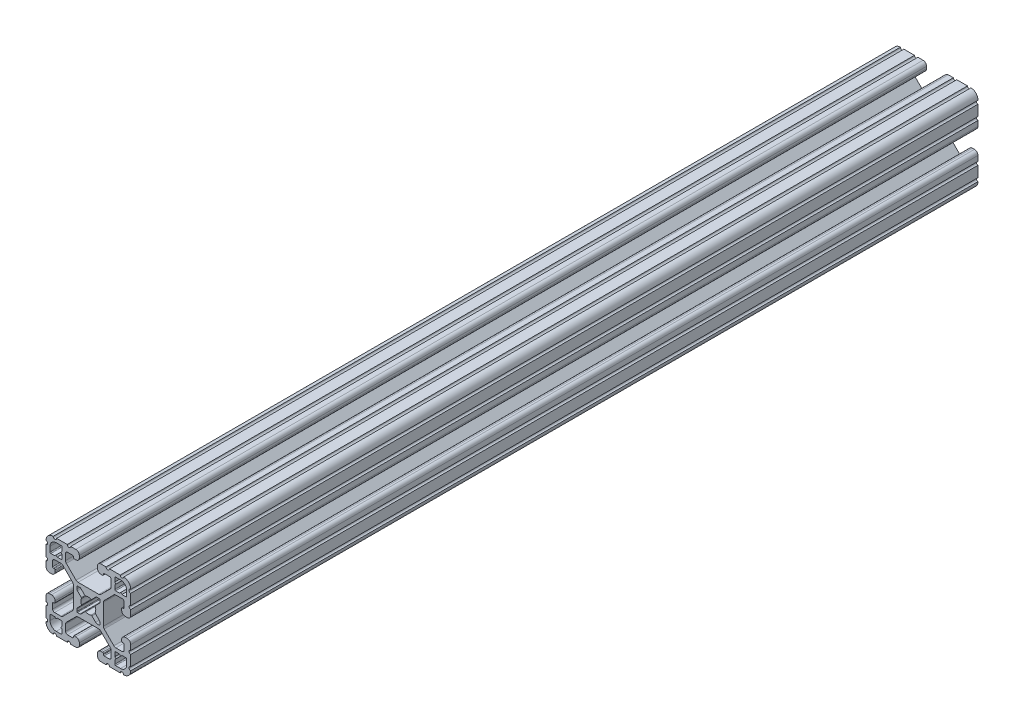
SolidWorks part; units mm, degrees
ref_plane "Front Plane" through (0, 0, 0) normal (0, 0, 1) x (1, 0, 0)
ref_plane "Top Plane" through (0, 0, 0) normal (0, 1, 0) x (1, 0, 0)
ref_plane "Right Plane" through (0, 0, 0) normal (1, 0, 0) x (0, 0, -1)
sketch "Sketch1" plane through (0, 0, 0) normal (0, 0, 1) x (1, 0, 0)
  line L0 (1.5823, 3.1988) -> (3.2921, 4.9085)
  line L1 (3.9207, 5.1689) -> (4.9149, 5.1689)
  line L2 (5.1689, 4.9149) -> (5.1689, 3.9207)
  line L3 (4.9085, 3.2921) -> (3.1988, 1.5823)
  line L4 (3.1988, -1.5823) -> (4.9085, -3.2921)
  line L5 (5.1689, -3.9207) -> (5.1689, -4.9149)
  line L6 (4.9149, -5.1689) -> (3.9207, -5.1689)
  line L7 (3.2921, -4.9085) -> (1.5823, -3.1988)
  line L8 (-1.5823, -3.1988) -> (-3.2921, -4.9085)
  line L9 (-3.9207, -5.1689) -> (-4.9149, -5.1689)
  line L10 (-5.1689, -4.9149) -> (-5.1689, -3.9207)
  line L11 (-4.9085, -3.2921) -> (-3.1988, -1.5823)
  line L12 (-3.1988, 1.5823) -> (-4.9085, 3.2921)
  line L13 (-5.1689, 3.9207) -> (-5.1689, 4.9149)
  line L14 (-4.9149, 5.1689) -> (-3.9207, 5.1689)
  line L15 (-3.2921, 4.9085) -> (-1.5823, 3.1988)
  line L16 (-11.8669, 14.0194) -> (-11.8669, 12.2479)
  line L17 (-12.2479, 11.8669) -> (-14.0195, 11.8669)
  line L18 (-14.0213, 11.8676) -> (-14.5575, 12.4039)
  line L19 (-14.5611, 12.4039) -> (-15.0973, 11.8676)
  line L20 (-15.0991, 11.8669) -> (-16.8707, 11.8669)
  line L21 (-17.2517, 12.2479) -> (-17.2517, 14.4577)
  line L22 (-14.4577, 17.2517) -> (-12.2479, 17.2517)
  line L23 (-11.8669, 16.8707) -> (-11.8669, 15.0991)
  line L24 (-11.8676, 15.0973) -> (-12.4039, 14.5611)
  line L25 (-12.4039, 14.5575) -> (-11.8676, 14.0212)
  line L26 (-14.0194, -11.8669) -> (-12.2479, -11.8669)
  line L27 (-11.8669, -12.2479) -> (-11.8669, -14.0195)
  line L28 (-11.8676, -14.0213) -> (-12.4039, -14.5575)
  line L29 (-12.4039, -14.5611) -> (-11.8676, -15.0973)
  line L30 (-11.8669, -15.0991) -> (-11.8669, -16.8707)
  line L31 (-12.2479, -17.2517) -> (-14.4577, -17.2517)
  line L32 (-17.2517, -14.4577) -> (-17.2517, -12.2479)
  line L33 (-16.8707, -11.8669) -> (-15.0991, -11.8669)
  line L34 (-15.0973, -11.8676) -> (-14.5611, -12.4039)
  line L35 (-14.5575, -12.4039) -> (-14.0212, -11.8676)
  line L36 (11.8669, -14.0194) -> (11.8669, -12.2479)
  line L37 (12.2479, -11.8669) -> (14.0195, -11.8669)
  line L38 (14.0213, -11.8676) -> (14.5575, -12.4039)
  line L39 (14.5611, -12.4039) -> (15.0973, -11.8676)
  line L40 (15.0991, -11.8669) -> (16.8707, -11.8669)
  line L41 (17.2517, -12.2479) -> (17.2517, -14.4577)
  line L42 (14.4577, -17.2517) -> (12.2479, -17.2517)
  line L43 (11.8669, -16.8707) -> (11.8669, -15.0991)
  line L44 (11.8676, -15.0973) -> (12.4039, -14.5611)
  line L45 (12.4039, -14.5575) -> (11.8676, -14.0212)
  line L46 (14.0194, 11.8669) -> (12.2479, 11.8669)
  line L47 (11.8669, 12.2479) -> (11.8669, 14.0195)
  line L48 (11.8676, 14.0213) -> (12.4039, 14.5575)
  line L49 (12.4039, 14.5611) -> (11.8676, 15.0973)
  line L50 (11.8669, 15.0991) -> (11.8669, 16.8707)
  line L51 (12.2479, 17.2517) -> (14.4577, 17.2517)
  line L52 (17.2517, 14.4577) -> (17.2517, 12.2479)
  line L53 (16.8707, 11.8669) -> (15.0991, 11.8669)
  line L54 (15.0973, 11.8676) -> (14.5611, 12.4039)
  line L55 (14.5575, 12.4039) -> (14.0212, 11.8676)
  line L56 (6.3498, -14.9848) -> (5.6531, -14.9848)
  line L57 (4.0778, -16.5601) -> (4.0778, -17.4747)
  line L58 (5.6531, -19.05) -> (7.9756, -19.05)
  line L59 (9.4996, -19.05) -> (14.2981, -19.05)
  line L60 (19.05, -14.3256) -> (19.05, -9.4996)
  line L61 (19.05, -7.9756) -> (19.05, -5.6531)
  line L62 (17.4747, -4.0778) -> (16.5601, -4.0778)
  line L63 (14.9848, -5.6531) -> (14.9848, -6.3498)
  line L64 (15.3661, -6.731) -> (15.6969, -6.731)
  line L65 (16.0782, -7.1122) -> (16.0782, -9.3968)
  line L66 (15.1881, -10.287) -> (12.3526, -10.2871)
  line L67 (11.4535, -9.9142) -> (7.1147, -5.5659)
  line L68 (6.7437, -4.6689) -> (6.7437, 4.6414)
  line L69 (7.1147, 5.5384) -> (11.481, 9.9142)
  line L70 (12.38, 10.2871) -> (15.1881, 10.287)
  line L71 (16.0782, 9.3968) -> (16.0782, 7.1122)
  line L72 (15.6969, 6.731) -> (15.3661, 6.731)
  line L73 (14.9848, 6.3498) -> (14.9848, 5.6531)
  line L74 (16.5601, 4.0778) -> (17.4747, 4.0778)
  line L75 (19.05, 5.6531) -> (19.05, 7.9756)
  line L76 (19.05, 9.4996) -> (19.05, 14.2981)
  line L77 (14.3256, 19.05) -> (9.4996, 19.05)
  line L78 (7.9756, 19.05) -> (5.6531, 19.05)
  line L79 (4.0778, 17.4747) -> (4.0778, 16.5601)
  line L80 (5.6531, 14.9848) -> (6.3498, 14.9848)
  line L81 (6.731, 15.3661) -> (6.731, 15.6969)
  line L82 (7.1122, 16.0782) -> (9.3968, 16.0782)
  line L83 (10.287, 15.1881) -> (10.2871, 12.3526)
  line L84 (9.9142, 11.4535) -> (5.5659, 7.1147)
  line L85 (4.6689, 6.7437) -> (-4.6414, 6.7437)
  line L86 (-5.5384, 7.1147) -> (-9.9142, 11.481)
  line L87 (-10.2871, 12.38) -> (-10.287, 15.1881)
  line L88 (-9.3968, 16.0782) -> (-7.1122, 16.0782)
  line L89 (-6.731, 15.6969) -> (-6.731, 15.3661)
  line L90 (-6.3498, 14.9848) -> (-5.6531, 14.9848)
  line L91 (-4.0778, 16.5601) -> (-4.0778, 17.4747)
  line L92 (-5.6531, 19.05) -> (-7.9756, 19.05)
  line L93 (-9.4996, 19.05) -> (-14.2981, 19.05)
  line L94 (-19.05, 14.3256) -> (-19.05, 9.4996)
  line L95 (-19.05, 7.9756) -> (-19.05, 5.6531)
  line L96 (-17.4747, 4.0778) -> (-16.5601, 4.0778)
  line L97 (-14.9848, 5.6531) -> (-14.9848, 6.3498)
  line L98 (-15.3661, 6.731) -> (-15.6969, 6.731)
  line L99 (-16.0782, 7.1122) -> (-16.0782, 9.3968)
  line L100 (-15.1881, 10.287) -> (-12.3526, 10.2871)
  line L101 (-11.4535, 9.9142) -> (-7.1147, 5.5659)
  line L102 (-6.7437, 4.6689) -> (-6.7437, -4.6414)
  line L103 (-7.1147, -5.5384) -> (-11.481, -9.9142)
  line L104 (-12.38, -10.2871) -> (-15.1881, -10.287)
  line L105 (-16.0782, -9.3968) -> (-16.0782, -7.1122)
  line L106 (-15.6969, -6.731) -> (-15.3661, -6.731)
  line L107 (-14.9848, -6.3498) -> (-14.9848, -5.6531)
  line L108 (-16.5601, -4.0778) -> (-17.4747, -4.0778)
  line L109 (-19.05, -5.6531) -> (-19.05, -7.9756)
  line L110 (-19.05, -9.4996) -> (-19.05, -14.2981)
  line L111 (-14.3256, -19.05) -> (-9.4996, -19.05)
  line L112 (-7.9756, -19.05) -> (-5.6531, -19.05)
  line L113 (-4.0778, -17.4747) -> (-4.0778, -16.5601)
  line L114 (-5.6531, -14.9848) -> (-6.3498, -14.9848)
  line L115 (-6.731, -15.3661) -> (-6.731, -15.6969)
  line L116 (-7.1122, -16.0782) -> (-9.3968, -16.0782)
  line L117 (-10.287, -15.1881) -> (-10.2871, -12.3526)
  line L118 (-9.9142, -11.4535) -> (-5.5659, -7.1147)
  line L119 (-4.6689, -6.7437) -> (4.6414, -6.7437)
  line L120 (5.5384, -7.1147) -> (9.9142, -11.481)
  line L121 (10.2871, -12.38) -> (10.287, -15.1881)
  line L122 (9.3968, -16.0782) -> (7.1122, -16.0782)
  line L123 (6.731, -15.6969) -> (6.731, -15.3661)
  arc A0 (1.178, 3.1119) -> (1.5823, 3.1988) centre (1.3129, 3.4682) ccw
  arc A1 (3.9207, 5.1689) -> (3.2921, 4.9085) centre (3.9207, 4.2799) ccw
  arc A2 (5.1689, 4.9149) -> (4.9149, 5.1689) centre (4.9149, 4.9149) ccw
  arc A3 (4.9085, 3.2921) -> (5.1689, 3.9207) centre (4.2799, 3.9207) ccw
  arc A4 (3.1988, 1.5823) -> (3.1119, 1.178) centre (3.4682, 1.3129) ccw
  arc A5 (3.1119, -1.178) -> (3.1119, 1.178) centre (0, 0) ccw
  arc A6 (3.1119, -1.178) -> (3.1988, -1.5823) centre (3.4682, -1.3129) ccw
  arc A7 (5.1689, -3.9207) -> (4.9085, -3.2921) centre (4.2799, -3.9207) ccw
  arc A8 (4.9149, -5.1689) -> (5.1689, -4.9149) centre (4.9149, -4.9149) ccw
  arc A9 (3.2921, -4.9085) -> (3.9207, -5.1689) centre (3.9207, -4.2799) ccw
  arc A10 (1.5823, -3.1988) -> (1.178, -3.1119) centre (1.3129, -3.4682) ccw
  arc A11 (-1.178, -3.1119) -> (1.178, -3.1119) centre (0, 0) ccw
  arc A12 (-1.178, -3.1119) -> (-1.5823, -3.1988) centre (-1.3129, -3.4682) ccw
  arc A13 (-3.9207, -5.1689) -> (-3.2921, -4.9085) centre (-3.9207, -4.2799) ccw
  arc A14 (-5.1689, -4.9149) -> (-4.9149, -5.1689) centre (-4.9149, -4.9149) ccw
  arc A15 (-4.9085, -3.2921) -> (-5.1689, -3.9207) centre (-4.2799, -3.9207) ccw
  arc A16 (-3.1988, -1.5823) -> (-3.1119, -1.178) centre (-3.4682, -1.3129) ccw
  arc A17 (-3.1119, 1.178) -> (-3.1119, -1.178) centre (0, 0) ccw
  arc A18 (-3.1119, 1.178) -> (-3.1988, 1.5823) centre (-3.4682, 1.3129) ccw
  arc A19 (-5.1689, 3.9207) -> (-4.9085, 3.2921) centre (-4.2799, 3.9207) ccw
  arc A20 (-4.9149, 5.1689) -> (-5.1689, 4.9149) centre (-4.9149, 4.9149) ccw
  arc A21 (-3.2921, 4.9085) -> (-3.9207, 5.1689) centre (-3.9207, 4.2799) ccw
  arc A22 (-1.5823, 3.1988) -> (-1.178, 3.1119) centre (-1.3129, 3.4682) ccw
  arc A23 (1.178, 3.1119) -> (-1.178, 3.1119) centre (0, 0) ccw
  arc A24 (-11.8669, 14.0194) -> (-11.8676, 14.0212) centre (-11.8694, 14.0194) ccw
  arc A25 (-12.2479, 11.8669) -> (-11.8669, 12.2479) centre (-12.2479, 12.2479) ccw
  arc A26 (-14.0213, 11.8676) -> (-14.0195, 11.8669) centre (-14.0195, 11.8694) ccw
  arc A27 (-14.5575, 12.4039) -> (-14.5611, 12.4039) centre (-14.5593, 12.4021) ccw
  arc A28 (-15.0991, 11.8669) -> (-15.0973, 11.8676) centre (-15.0991, 11.8694) ccw
  arc A29 (-17.2517, 12.2479) -> (-16.8707, 11.8669) centre (-16.8707, 12.2479) ccw
  arc A30 (-14.4577, 17.2517) -> (-17.2517, 14.4577) centre (-14.4577, 14.4577) ccw
  arc A31 (-11.8669, 16.8707) -> (-12.2479, 17.2517) centre (-12.2479, 16.8707) ccw
  arc A32 (-11.8676, 15.0973) -> (-11.8669, 15.0991) centre (-11.8694, 15.0991) ccw
  arc A33 (-12.4039, 14.5611) -> (-12.4039, 14.5575) centre (-12.4021, 14.5593) ccw
  arc A34 (-14.0194, -11.8669) -> (-14.0212, -11.8676) centre (-14.0194, -11.8694) ccw
  arc A35 (-11.8669, -12.2479) -> (-12.2479, -11.8669) centre (-12.2479, -12.2479) ccw
  arc A36 (-11.8676, -14.0213) -> (-11.8669, -14.0195) centre (-11.8694, -14.0195) ccw
  arc A37 (-12.4039, -14.5575) -> (-12.4039, -14.5611) centre (-12.4021, -14.5593) ccw
  arc A38 (-11.8669, -15.0991) -> (-11.8676, -15.0973) centre (-11.8694, -15.0991) ccw
  arc A39 (-12.2479, -17.2517) -> (-11.8669, -16.8707) centre (-12.2479, -16.8707) ccw
  arc A40 (-17.2517, -14.4577) -> (-14.4577, -17.2517) centre (-14.4577, -14.4577) ccw
  arc A41 (-16.8707, -11.8669) -> (-17.2517, -12.2479) centre (-16.8707, -12.2479) ccw
  arc A42 (-15.0973, -11.8676) -> (-15.0991, -11.8669) centre (-15.0991, -11.8694) ccw
  arc A43 (-14.5611, -12.4039) -> (-14.5575, -12.4039) centre (-14.5593, -12.4021) ccw
  arc A44 (11.8669, -14.0194) -> (11.8676, -14.0212) centre (11.8694, -14.0194) ccw
  arc A45 (12.2479, -11.8669) -> (11.8669, -12.2479) centre (12.2479, -12.2479) ccw
  arc A46 (14.0213, -11.8676) -> (14.0195, -11.8669) centre (14.0195, -11.8694) ccw
  arc A47 (14.5575, -12.4039) -> (14.5611, -12.4039) centre (14.5593, -12.4021) ccw
  arc A48 (15.0991, -11.8669) -> (15.0973, -11.8676) centre (15.0991, -11.8694) ccw
  arc A49 (17.2517, -12.2479) -> (16.8707, -11.8669) centre (16.8707, -12.2479) ccw
  arc A50 (14.4577, -17.2517) -> (17.2517, -14.4577) centre (14.4577, -14.4577) ccw
  arc A51 (11.8669, -16.8707) -> (12.2479, -17.2517) centre (12.2479, -16.8707) ccw
  arc A52 (11.8676, -15.0973) -> (11.8669, -15.0991) centre (11.8694, -15.0991) ccw
  arc A53 (12.4039, -14.5611) -> (12.4039, -14.5575) centre (12.4021, -14.5593) ccw
  arc A54 (14.0194, 11.8669) -> (14.0212, 11.8676) centre (14.0194, 11.8694) ccw
  arc A55 (11.8669, 12.2479) -> (12.2479, 11.8669) centre (12.2479, 12.2479) ccw
  arc A56 (11.8676, 14.0213) -> (11.8669, 14.0195) centre (11.8694, 14.0195) ccw
  arc A57 (12.4039, 14.5575) -> (12.4039, 14.5611) centre (12.4021, 14.5593) ccw
  arc A58 (11.8669, 15.0991) -> (11.8676, 15.0973) centre (11.8694, 15.0991) ccw
  arc A59 (12.2479, 17.2517) -> (11.8669, 16.8707) centre (12.2479, 16.8707) ccw
  arc A60 (17.2517, 14.4577) -> (14.4577, 17.2517) centre (14.4577, 14.4577) ccw
  arc A61 (16.8707, 11.8669) -> (17.2517, 12.2479) centre (16.8707, 12.2479) ccw
  arc A62 (15.0973, 11.8676) -> (15.0991, 11.8669) centre (15.0991, 11.8694) ccw
  arc A63 (14.5611, 12.4039) -> (14.5575, 12.4039) centre (14.5593, 12.4021) ccw
  arc A64 (6.731, -15.3661) -> (6.3498, -14.9848) centre (6.35, -15.3658) ccw
  arc A65 (5.6531, -14.9848) -> (4.0778, -16.5601) centre (5.6526, -16.5596) ccw
  arc A66 (4.0778, -17.4747) -> (5.6531, -19.05) centre (5.6526, -17.4752) ccw
  arc A67 (9.4996, -19.05) -> (7.9756, -19.05) centre (8.7376, -19.05) ccw
  arc A68 (15.8221, -19.0496) -> (14.2981, -19.05) centre (15.0601, -19.05) ccw
  arc A69 (15.8221, -19.0496) -> (19.0499, -15.8496) centre (15.875, -15.875) ccw
  arc A70 (19.05, -14.3256) -> (19.0499, -15.8496) centre (19.05, -15.0876) ccw
  arc A71 (19.05, -7.9756) -> (19.05, -9.4996) centre (19.05, -8.7376) ccw
  arc A72 (19.05, -5.6531) -> (17.4747, -4.0778) centre (17.4752, -5.6526) ccw
  arc A73 (16.5601, -4.0778) -> (14.9848, -5.6531) centre (16.5596, -5.6526) ccw
  arc A74 (14.9848, -6.3498) -> (15.3661, -6.731) centre (15.3658, -6.35) ccw
  arc A75 (16.0782, -7.1122) -> (15.6969, -6.731) centre (15.6972, -7.112) ccw
  arc A76 (15.1881, -10.287) -> (16.0782, -9.3968) centre (15.1892, -9.398) ccw
  arc A77 (11.4535, -9.9142) -> (12.3526, -10.2871) centre (12.3525, -9.0171) ccw
  arc A78 (6.7437, -4.6689) -> (7.1147, -5.5659) centre (8.0137, -4.6689) ccw
  arc A79 (7.1147, 5.5384) -> (6.7437, 4.6414) centre (8.0137, 4.6414) ccw
  arc A80 (12.38, 10.2871) -> (11.481, 9.9142) centre (12.38, 9.0171) ccw
  arc A81 (16.0782, 9.3968) -> (15.1881, 10.287) centre (15.1892, 9.398) ccw
  arc A82 (15.6969, 6.731) -> (16.0782, 7.1122) centre (15.6972, 7.112) ccw
  arc A83 (15.3661, 6.731) -> (14.9848, 6.3498) centre (15.3658, 6.35) ccw
  arc A84 (14.9848, 5.6531) -> (16.5601, 4.0778) centre (16.5596, 5.6526) ccw
  arc A85 (17.4747, 4.0778) -> (19.05, 5.6531) centre (17.4752, 5.6526) ccw
  arc A86 (19.05, 9.4996) -> (19.05, 7.9756) centre (19.05, 8.7376) ccw
  arc A87 (19.0496, 15.8221) -> (19.05, 14.2981) centre (19.05, 15.0601) ccw
  arc A88 (19.0496, 15.8221) -> (15.8496, 19.0499) centre (15.875, 15.875) ccw
  arc A89 (14.3256, 19.05) -> (15.8496, 19.0499) centre (15.0876, 19.05) ccw
  arc A90 (7.9756, 19.05) -> (9.4996, 19.05) centre (8.7376, 19.05) ccw
  arc A91 (5.6531, 19.05) -> (4.0778, 17.4747) centre (5.6526, 17.4752) ccw
  arc A92 (4.0778, 16.5601) -> (5.6531, 14.9848) centre (5.6526, 16.5596) ccw
  arc A93 (6.3498, 14.9848) -> (6.731, 15.3661) centre (6.35, 15.3658) ccw
  arc A94 (7.1122, 16.0782) -> (6.731, 15.6969) centre (7.112, 15.6972) ccw
  arc A95 (10.287, 15.1881) -> (9.3968, 16.0782) centre (9.398, 15.1892) ccw
  arc A96 (9.9142, 11.4535) -> (10.2871, 12.3526) centre (9.0171, 12.3525) ccw
  arc A97 (4.6689, 6.7437) -> (5.5659, 7.1147) centre (4.6689, 8.0137) ccw
  arc A98 (-5.5384, 7.1147) -> (-4.6414, 6.7437) centre (-4.6414, 8.0137) ccw
  arc A99 (-10.2871, 12.38) -> (-9.9142, 11.481) centre (-9.0171, 12.38) ccw
  arc A100 (-9.3968, 16.0782) -> (-10.287, 15.1881) centre (-9.398, 15.1892) ccw
  arc A101 (-6.731, 15.6969) -> (-7.1122, 16.0782) centre (-7.112, 15.6972) ccw
  arc A102 (-6.731, 15.3661) -> (-6.3498, 14.9848) centre (-6.35, 15.3658) ccw
  arc A103 (-5.6531, 14.9848) -> (-4.0778, 16.5601) centre (-5.6526, 16.5596) ccw
  arc A104 (-4.0778, 17.4747) -> (-5.6531, 19.05) centre (-5.6526, 17.4752) ccw
  arc A105 (-9.4996, 19.05) -> (-7.9756, 19.05) centre (-8.7376, 19.05) ccw
  arc A106 (-15.8221, 19.0496) -> (-14.2981, 19.05) centre (-15.0601, 19.05) ccw
  arc A107 (-15.8221, 19.0496) -> (-19.0499, 15.8496) centre (-15.875, 15.875) ccw
  arc A108 (-19.05, 14.3256) -> (-19.0499, 15.8496) centre (-19.05, 15.0876) ccw
  arc A109 (-19.05, 7.9756) -> (-19.05, 9.4996) centre (-19.05, 8.7376) ccw
  arc A110 (-19.05, 5.6531) -> (-17.4747, 4.0778) centre (-17.4752, 5.6526) ccw
  arc A111 (-16.5601, 4.0778) -> (-14.9848, 5.6531) centre (-16.5596, 5.6526) ccw
  arc A112 (-14.9848, 6.3498) -> (-15.3661, 6.731) centre (-15.3658, 6.35) ccw
  arc A113 (-16.0782, 7.1122) -> (-15.6969, 6.731) centre (-15.6972, 7.112) ccw
  arc A114 (-15.1881, 10.287) -> (-16.0782, 9.3968) centre (-15.1892, 9.398) ccw
  arc A115 (-11.4535, 9.9142) -> (-12.3526, 10.2871) centre (-12.3525, 9.0171) ccw
  arc A116 (-6.7437, 4.6689) -> (-7.1147, 5.5659) centre (-8.0137, 4.6689) ccw
  arc A117 (-7.1147, -5.5384) -> (-6.7437, -4.6414) centre (-8.0137, -4.6414) ccw
  arc A118 (-12.38, -10.2871) -> (-11.481, -9.9142) centre (-12.38, -9.0171) ccw
  arc A119 (-16.0782, -9.3968) -> (-15.1881, -10.287) centre (-15.1892, -9.398) ccw
  arc A120 (-15.6969, -6.731) -> (-16.0782, -7.1122) centre (-15.6972, -7.112) ccw
  arc A121 (-15.3661, -6.731) -> (-14.9848, -6.3498) centre (-15.3658, -6.35) ccw
  arc A122 (-14.9848, -5.6531) -> (-16.5601, -4.0778) centre (-16.5596, -5.6526) ccw
  arc A123 (-17.4747, -4.0778) -> (-19.05, -5.6531) centre (-17.4752, -5.6526) ccw
  arc A124 (-19.05, -9.4996) -> (-19.05, -7.9756) centre (-19.05, -8.7376) ccw
  arc A125 (-19.0496, -15.8221) -> (-19.05, -14.2981) centre (-19.05, -15.0601) ccw
  arc A126 (-19.0496, -15.8221) -> (-15.8496, -19.0499) centre (-15.875, -15.875) ccw
  arc A127 (-14.3256, -19.05) -> (-15.8496, -19.0499) centre (-15.0876, -19.05) ccw
  arc A128 (-7.9756, -19.05) -> (-9.4996, -19.05) centre (-8.7376, -19.05) ccw
  arc A129 (-5.6531, -19.05) -> (-4.0778, -17.4747) centre (-5.6526, -17.4752) ccw
  arc A130 (-4.0778, -16.5601) -> (-5.6531, -14.9848) centre (-5.6526, -16.5596) ccw
  arc A131 (-6.3498, -14.9848) -> (-6.731, -15.3661) centre (-6.35, -15.3658) ccw
  arc A132 (-7.1122, -16.0782) -> (-6.731, -15.6969) centre (-7.112, -15.6972) ccw
  arc A133 (-10.287, -15.1881) -> (-9.3968, -16.0782) centre (-9.398, -15.1892) ccw
  arc A134 (-9.9142, -11.4535) -> (-10.2871, -12.3526) centre (-9.0171, -12.3525) ccw
  arc A135 (-4.6689, -6.7437) -> (-5.5659, -7.1147) centre (-4.6689, -8.0137) ccw
  arc A136 (5.5384, -7.1147) -> (4.6414, -6.7437) centre (4.6414, -8.0137) ccw
  arc A137 (10.2871, -12.38) -> (9.9142, -11.481) centre (9.0171, -12.38) ccw
  arc A138 (9.3968, -16.0782) -> (10.287, -15.1881) centre (9.398, -15.1892) ccw
  arc A139 (6.731, -15.6969) -> (7.1122, -16.0782) centre (7.112, -15.6972) ccw
extrude "Extrude1" add sketch "Sketch1" against normal blind 381
